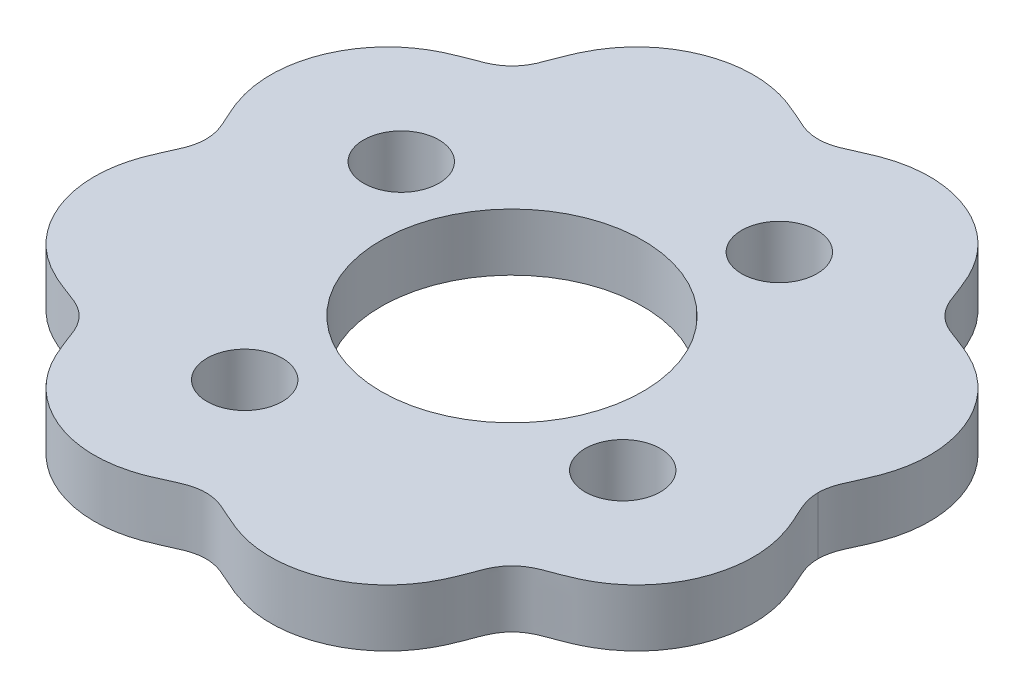
SolidWorks part; units mm, degrees
material "POM Acetal Copolymer"
ref_plane "Front Plane" through (0, 0, 0) normal (0, 0, 1) x (1, 0, 0)
ref_plane "Top Plane" through (0, 0, 0) normal (0, 1, 0) x (1, 0, 0)
ref_plane "Right Plane" through (0, 0, 0) normal (1, 0, 0) x (0, 0, -1)
sketch "Sketch2" plane through (0, 0, 0) normal (0, 1, 0) x (1, 0, 0)
  line L0 (-37.5, 0) -> (37.5, 0) construction
  spline S0 degree 4 number of poles 176 (36.9805, 20.0285) -> (-36.9805, 20.0285) construction
  spline S1 degree 4 number of poles 106 (37.5, 0) -> (-37.5, 0)
  spline S2 degree 4 number of poles 106 (37.5, 0) -> (-37.5, 0)
extrude "Boss-Extrude1" add sketch "Sketch2" along normal blind 7 contours S2 S1
sketch "Sketch3" plane through (0, 7, 0) normal (0, 1, 0) x (1, 0, 0)
  line L0 (0, 0) -> (39.2649, -16.264) construction
  circle A0 centre (0, 0) radius 16
  circle A1 centre (23.097, -9.5671) radius 4.5
  circle A3 centre (-9.5671, -23.097) radius 4.5
  circle A4 centre (-23.097, 9.5671) radius 4.5
  circle A5 centre (9.5671, 23.097) radius 4.5
  spline S0 degree 4 number of poles 106 (37.5, 0) -> (-37.5, 0) construction
  point P18 (0, 0)
  dimension "D1" = 32
  dimension "D2" = 9
  dimension "D4" = 25
  dimension "D5" = 4
extrude "Cut-Extrude1" cut sketch "Sketch3" against normal blind 7
sketch "Sketch4" plane through (0, 0, 0) normal (0, -1, 0) x (1, 0, 0)
  spline S4 degree 3 number of poles 181 (-37.4, 0) -> (37.4, 0)
  spline S5 degree 3 number of poles 174 (37.4, 0) -> (-37.4, 0)
  spline S6 degree 3 number of poles 181 (-37.4, 0) -> (37.4, 0)
  spline S7 degree 3 number of poles 174 (37.4, 0) -> (-37.4, 0)
  spline S9 degree 3 number of poles 172 (37.6, 0) -> (-37.6, 0)
  spline S10 degree 3 number of poles 172 (-37.6, 0) -> (37.6, 0)
  spline S11 degree 3 number of poles 172 (37.6, 0) -> (-37.6, 0)
  spline S12 degree 3 number of poles 172 (-37.6, 0) -> (37.6, 0)
  dimension "D1" = 0.1
  dimension "D2" = 0.1
sketch "Sketch5" plane through (0, 0, 0) normal (0, -1, 0) x (1, 0, 0)
  circle A2 centre (-9.5671, 23.097) radius 4.5
  circle A3 centre (-9.5671, 23.097) radius 4.5
  circle A5 centre (23.097, 9.5671) radius 4.5
  circle A6 centre (23.097, 9.5671) radius 4.5
  circle A8 centre (-23.097, -9.5671) radius 4.5
  circle A9 centre (-23.097, -9.5671) radius 4.5
  circle A10 centre (-23.097, -9.5671) radius 4.6
  circle A11 centre (9.5671, -23.097) radius 4.5
  circle A12 centre (9.5671, -23.097) radius 4.5
  circle A13 centre (9.5671, -23.097) radius 4.6
  circle A14 centre (23.097, 9.5671) radius 4.6
  circle A15 centre (-9.5671, 23.097) radius 4.6
  dimension "D1" = 0
  dimension "D2" = 0
  dimension "D3" = 0
  dimension "D4" = 0
  dimension "D5" = 0.1
  dimension "D6" = 0.1
  dimension "D7" = 0.1
  dimension "D8" = 0.1
extrude "Cut-Extrude2" cut sketch "Sketch4" against normal up to surface (7 mm away) up to face at (9.5671, 7, -18.597)
extrude "Cut-Extrude3" cut sketch "Sketch5" against normal up to surface (7 mm away) up to face at (0, 7, 16)
